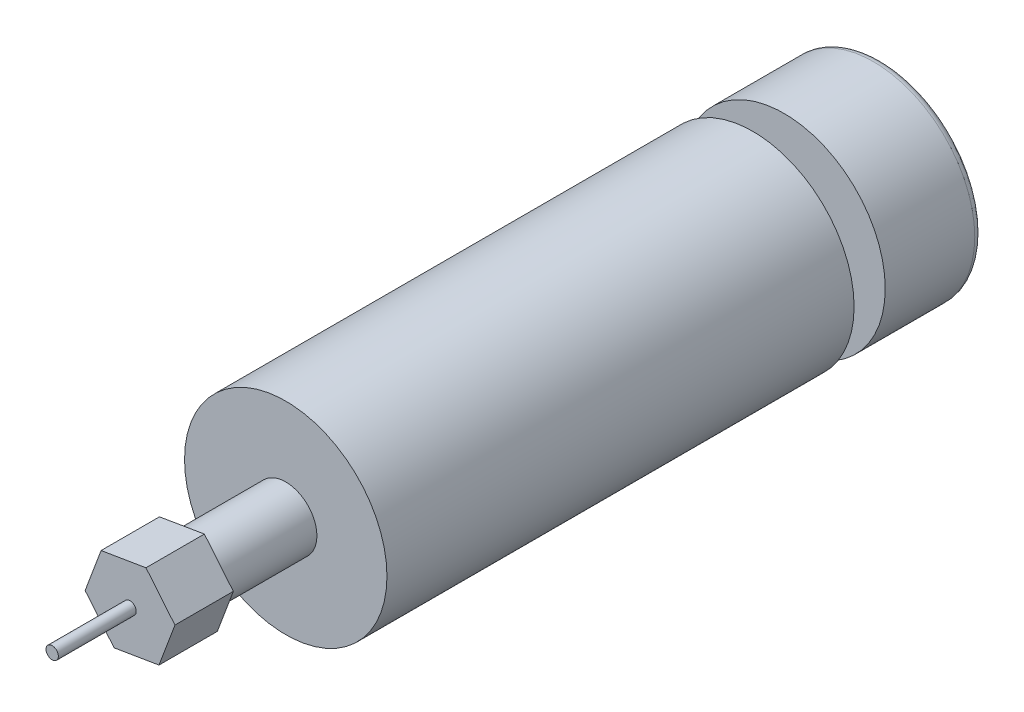
SolidWorks part; units mm, degrees
ref_plane "Спереди" through (0, 0, 0) normal (0, 0, 1) x (1, 0, 0)
ref_plane "Сверху" through (0, 0, 0) normal (0, 1, 0) x (1, 0, 0)
ref_plane "Справа" through (0, 0, 0) normal (1, 0, 0) x (0, 0, -1)
sketch "Эскиз1" plane through (0, 0, 0) normal (0, 0, 1) x (1, 0, 0)
  circle A0 centre (0, 0) radius 26
extrude "Бобышка-Вытянуть1" add sketch "Эскиз1" along normal blind 120
sketch "Эскиз2" plane through (0, 0, 0) normal (0, 0, -1) x (-1, 0, 0)
  circle A0 centre (0, 0) radius 26
extrude "Бобышка-Вытянуть2" add sketch "Эскиз2" along normal blind 25 from offset 8 separate body
fillet "Скругление1" radius 2 1 edges at (-26, 0, -33)
sketch "Эскиз3" plane through (0, 0, 120) normal (0, 0, 1) x (1, 0, 0)
  circle A0 centre (0, 0) radius 8
extrude "Бобышка-Вытянуть3" add sketch "Эскиз3" along normal blind 40
sketch "Эскиз4" plane through (0, 0, 160) normal (0, 0, 1) x (1, 0, 0)
  line L1 (11.5341, 1.9302) -> (4.0955, 10.9539)
  line L2 (4.0955, 10.9539) -> (-7.4386, 9.0238)
  line L3 (-7.4386, 9.0238) -> (-11.5341, -1.9302)
  line L4 (-11.5341, -1.9302) -> (-4.0955, -10.9539)
  line L5 (-4.0955, -10.9539) -> (7.4386, -9.0238)
  line L6 (7.4386, -9.0238) -> (11.5341, 1.9302)
  circle A0 centre (0, 0) radius 10.1278 construction
extrude "Бобышка-Вытянуть4" add sketch "Эскиз4" against normal blind 15
sketch "Эскиз5" plane through (0, 0, 160) normal (0, 0, -1) x (-1, 0, 0)
  circle A0 centre (0, 0) radius 1.5875
  dimension "D1" = 3.175
extrude "Бобышка-Вытянуть5" add sketch "Эскиз5" against normal blind 20
sketch "Эскиз7" plane through (0, 0, 0) normal (0, 0, -1) x (-1, 0, 0)
  circle A0 centre (0, 0) radius 4
extrude "Бобышка-Вытянуть6" add sketch "Эскиз7" along normal blind 6
